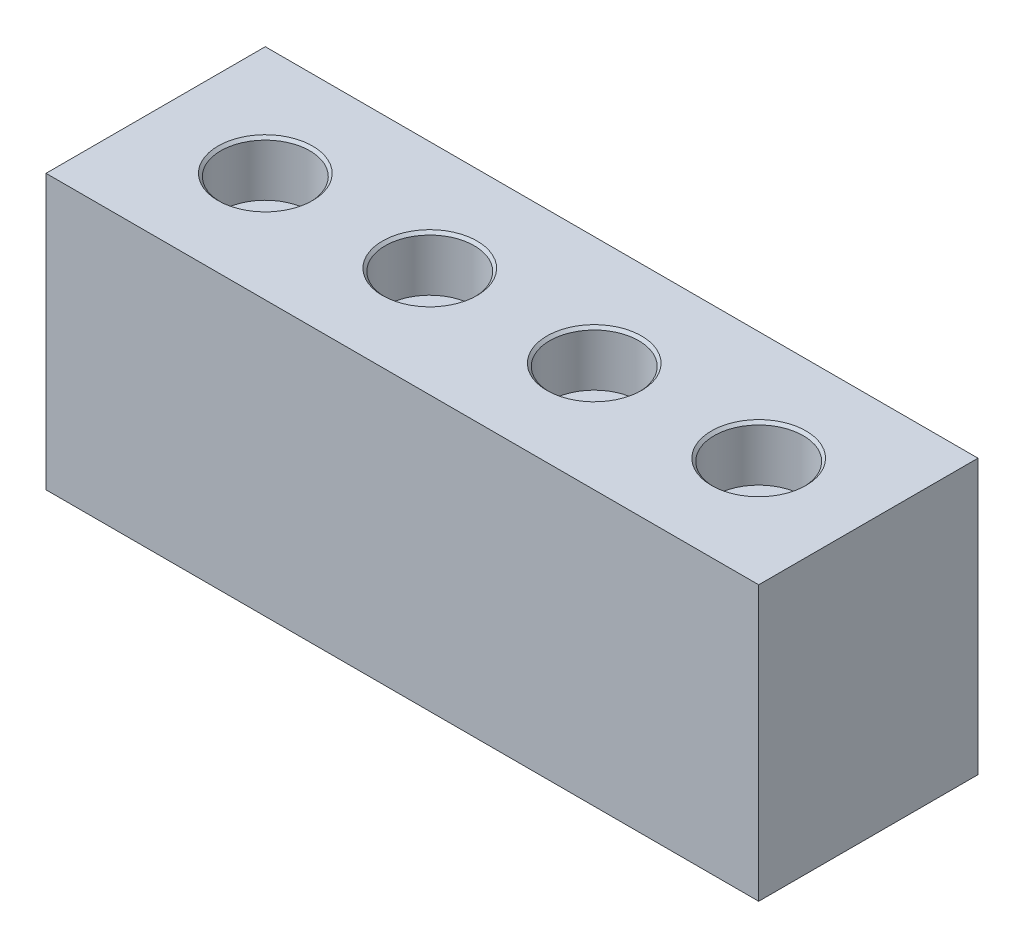
SolidWorks part; units mm, degrees
ref_plane "Front Plane" through (0, 0, 0) normal (0, 0, 1) x (1, 0, 0)
ref_plane "Top Plane" through (0, 0, 0) normal (0, 1, 0) x (1, 0, 0)
ref_plane "Right Plane" through (0, 0, 0) normal (1, 0, 0) x (0, 0, -1)
sketch "Sketch1" plane through (0, 0, 0) normal (0, 0, 1) x (1, 0, 0)
  line L1 (82.55, -31.75) -> (-82.55, -31.75)
  line L2 (82.55, -31.75) -> (82.55, 31.75)
  line L3 (82.55, 31.75) -> (-82.55, 31.75)
  line L4 (-82.55, -31.75) -> (-82.55, 31.75)
  line L5 (82.55, -31.75) -> (-82.55, 31.75) construction
  line L6 (82.55, 31.75) -> (-82.55, -31.75) construction
  point P0 (0, 0)
  dimension "D1" = 165.1
  dimension "D2" = 63.5
extrude "Boss-Extrude1" add sketch "Sketch1" along normal mid plane 50.8
sketch "Sketch2" plane through (0, 31.75, 0) normal (0, 1, 0) x (1, 0, 0)
  line L0 (-57.15, 49.8686) -> (-57.15, -38.2077) construction
  line L1 (-82.55, -25.4) -> (-82.55, 25.4) construction
  line L2 (82.55, 25.4) -> (-82.55, 25.4) construction
  point P4 (-57.15, 0)
  dimension "D1" = 25.4
  dimension "D2" = 25.4
hole_wizard "CBORE for 1/2 Socket Head Cap Screw2" positions "3DSketch2" profile "Sketch4" counterbore size "1/2" standard "ANSI Inch"
sketch3d "3DSketch2"
  point P0 (-57.15, 31.75, 0)
sketch "Sketch4" plane through (-57.15, 31.75, 0) normal (1, 0, 0) x (0, 0, 1)
  line L0 (0, 0) -> (0, 54.8535)
  line L1 (0, 54.8535) -> (6.7462, 50.8)
  line L2 (6.7462, 50.8) -> (6.7462, 12.7)
  line L3 (6.7462, 12.7) -> (10.3187, 12.7)
  line L5 (10.3187, 12.7) -> (10.3187, 0.635)
  line L6 (10.3187, 0.635) -> (10.9537, 0)
  line L7 (10.9537, 0) -> (0, 0)
  line L8 (-10.3187, 0.635) -> (-10.9537, 0) construction
  line L10 (0, 54.8535) -> (-6.7462, 50.8) construction
  line L11 (0, -6.35) -> (0, 107.95) construction
  dimension "Hole Dia." = 13.4925
  dimension "Hole Depth" = 50.8
  dimension "C'Bore Dia." = 20.6375
  dimension "C'Bore Depth" = 12.7
  dimension "Near C'Sink Dia." = 21.9075
  dimension "Near C'Sink Angle" = 90
  dimension "Drill Angle" = 118
pattern_linear "LPattern1" count 4 spacing 38.1 along (1, 0, 0) of "CBORE for 1/2 Socket Head Cap Screw2"
